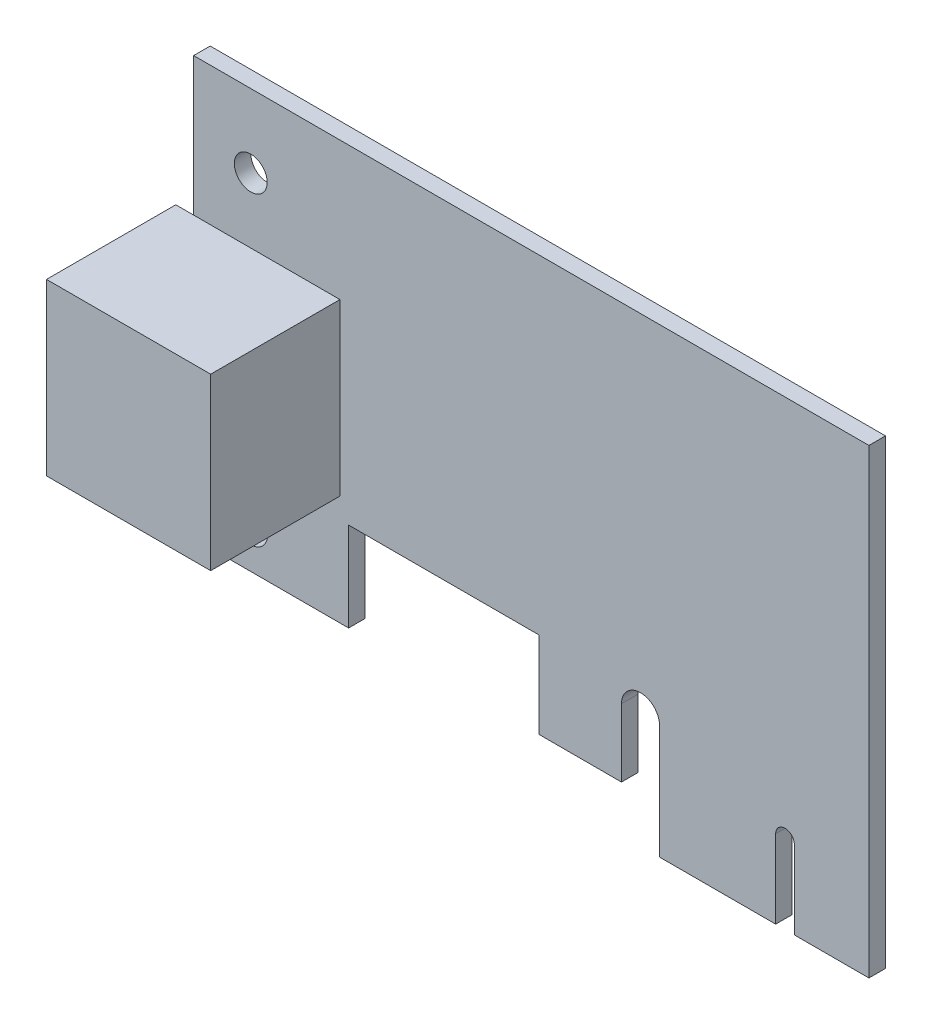
SolidWorks part; units mm, degrees
ref_plane "Front Plane" through (0, 0, 0) normal (0, 0, 1) x (1, 0, 0)
ref_plane "Top Plane" through (0, 0, 0) normal (0, 1, 0) x (1, 0, 0)
ref_plane "Right Plane" through (0, 0, 0) normal (1, 0, 0) x (0, 0, -1)
sketch "Sketch2" plane through (0, 0, 0) normal (0, 0, 1) x (1, 0, 0)
  line L0 (0, 4.1529) -> (14.986, 4.1529)
  line L1 (45.0596, 0) -> (56.2864, 0)
  line L2 (0, 4.1529) -> (0, 44.6024)
  line L3 (0, 44.6024) -> (65.3034, 44.6024)
  line L4 (65.3034, 0) -> (65.3034, 44.6024)
  line L5 (14.986, 4.1529) -> (14.986, 12.7762)
  line L6 (14.986, 12.7762) -> (33.3756, 12.7762)
  line L7 (33.3756, 12.7762) -> (33.3756, 4.445)
  line L8 (33.3756, 4.445) -> (41.3766, 4.445)
  line L9 (41.3766, 4.445) -> (41.3766, 11.0109)
  line L11 (45.0596, 11.0109) -> (45.0596, 0)
  line L12 (56.2864, 0) -> (56.2864, 7.5819)
  line L14 (58.0898, 7.5819) -> (58.0898, 0)
  line L15 (58.0898, 0) -> (65.3034, 0)
  arc A0 (58.0898, 7.5819) -> (56.2864, 7.5819) centre (57.1881, 7.5819) ccw
  arc A1 (45.0596, 11.0109) -> (41.3766, 11.0109) centre (43.2181, 11.0109) ccw
  circle A2 centre (5.5245, 37.5285) radius 1.5875
  circle A3 centre (5.55, 7.9883) radius 1.5875
  point P15 (43.2181, 12.8524)
  point P19 (57.1881, 8.4836)
  dimension "D19" = 3.175
  dimension "D1" = 65.3034
  dimension "D2" = 44.6024
  dimension "D3" = 40.4495
  dimension "D4" = 14.986
  dimension "D5" = 31.8262
  dimension "D6" = 8.001
  dimension "D7" = 3.683
  dimension "D8" = 40.1574
  dimension "D9" = 18.3896
  dimension "D10" = 31.75
  dimension "D11" = 11.2268
  dimension "D12" = 7.2136
  dimension "D13" = 1.8034
  dimension "D14" = 36.1188
  dimension "D15" = 5.5245
  dimension "D16" = 7.0739
  dimension "D17" = 5.55
  dimension "D18" = 36.6141
extrude "Boss-Extrude1" add sketch "Sketch2" along normal blind 1.6
sketch "Sketch3" plane through (0, 0, 1.6) normal (0, 0, 1) x (1, 0, 0)
  line L0 (65.3034, 44.6024) -> (0, 44.6024) construction
  line L1 (-1.7272, 31.242) -> (14.1478, 31.242)
  line L2 (-1.7272, 31.242) -> (-1.7272, 14.7828)
  line L3 (-1.7272, 14.7828) -> (14.1478, 14.7828)
  line L4 (14.1478, 31.242) -> (14.1478, 14.7828)
  line L5 (0, 44.6024) -> (0, 4.1529) construction
  dimension "D1" = 15.875
  dimension "D2" = 16.4592
  dimension "D3" = 13.3604
  dimension "D4" = 1.7272
extrude "Boss-Extrude2" add sketch "Sketch3" along normal blind 12.5
